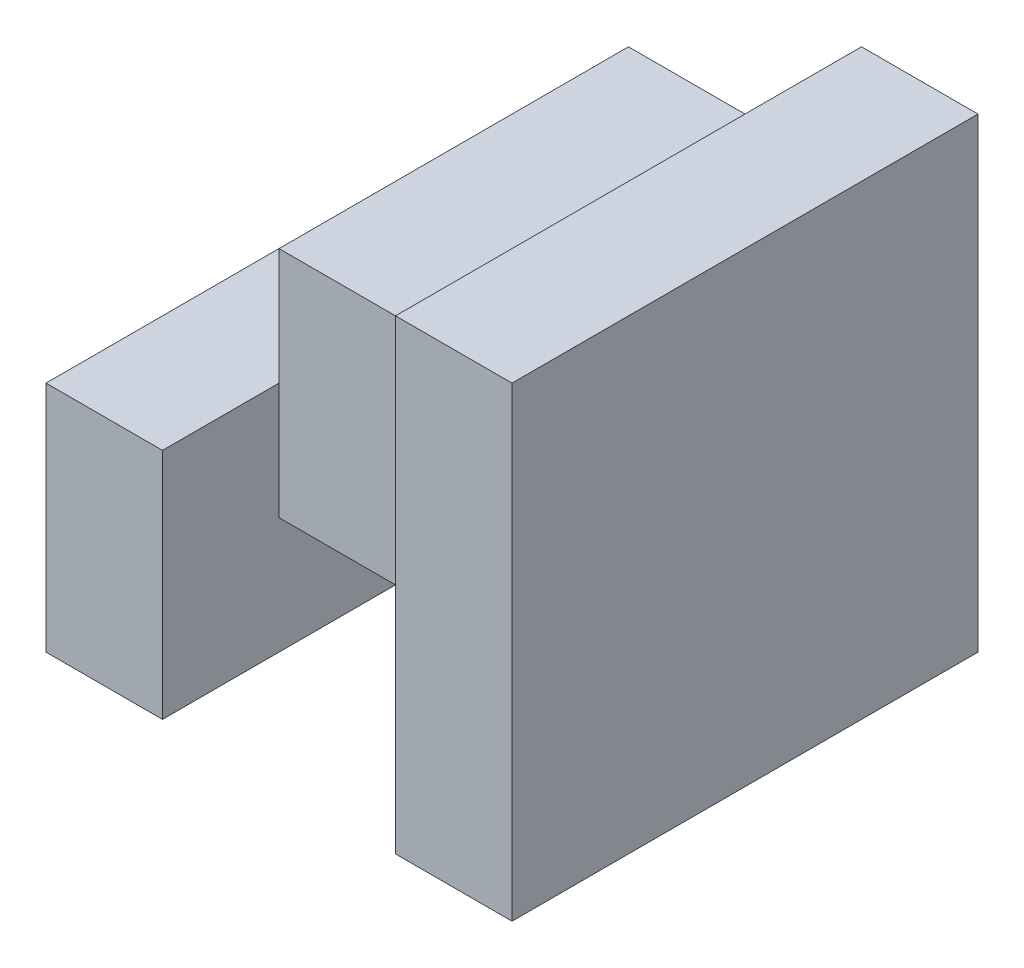
SolidWorks part; units mm, degrees
ref_plane "Front" through (0, 0, 0) normal (0, 0, 1) x (1, 0, 0)
ref_plane "Top" through (0, 0, 0) normal (0, 1, 0) x (1, 0, 0)
ref_plane "Right" through (0, 0, 0) normal (1, 0, 0) x (0, 0, -1)
sketch "Sketch1" plane through (0, 0, 0) normal (0, 0, 1) x (1, 0, 0)
  line L0 (0, 0) -> (0, 2)
  line L1 (0, 2) -> (1, 2)
  line L2 (1, 2) -> (1, 3)
  line L3 (1, 3) -> (3, 3)
  line L4 (3, 3) -> (3, 4)
  line L5 (3, 4) -> (4, 4)
  line L6 (4, 4) -> (4, 0)
  line L7 (4, 0) -> (3, 0)
  line L8 (3, 0) -> (3, 1)
  line L9 (3, 1) -> (1, 1)
  line L10 (1, 1) -> (1, 0)
  line L11 (1, 0) -> (0, 0)
  dimension "D1" = 4
  dimension "D2" = 1
  dimension "D3" = 1
  dimension "D4" = 1
  dimension "D5" = 1
  dimension "D6" = 2
  dimension "D7" = 1
  dimension "D8" = 1
  dimension "D9" = 2
extrude "Boss-Extrude1" add sketch "Sketch1" along normal blind 4
sketch "Sketch2" plane through (0, 0, 4) normal (0, 0, 1) x (1, 0, 0)
  line L1 (1, 3) -> (3, 3)
  line L2 (1, 3) -> (1, 0)
  line L3 (1, 0) -> (3, 0)
  line L4 (3, 3) -> (3, 0)
extrude "Cut-Extrude1" cut sketch "Sketch2" against normal blind 1
